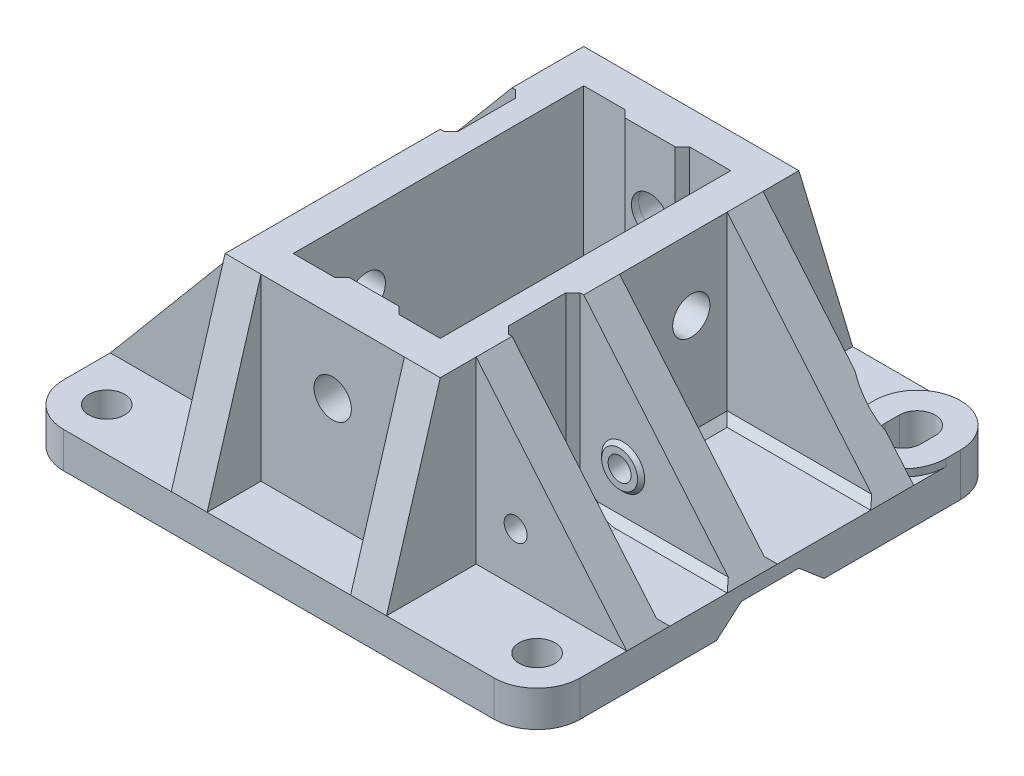
SolidWorks part; units mm, degrees
ref_plane "Front Plane" through (0, 0, 0) normal (0, 0, 1) x (1, 0, 0)
ref_plane "Top Plane" through (0, 0, 0) normal (0, 1, 0) x (1, 0, 0)
ref_plane "Right Plane" through (0, 0, 0) normal (1, 0, 0) x (0, 0, -1)
sketch "Sketch1" plane through (0, 0, 0) normal (0, 1, 0) x (1, 0, 0)
  line L0 (0, 0) -> (0, 65)
  line L1 (0, 0) -> (72, 0)
  line L2 (0, 65) -> (72, 65)
  line L3 (72, 0) -> (72, 65)
  dimension "D1" = 72
  dimension "D2" = 65
extrude "Boss-Extrude1" add sketch "Sketch1" along normal blind 5
sketch "Sketch2" plane through (0, 5, 0) normal (0, 1, 0) x (1, 0, 0)
  line L0 (21, 57.5) -> (21, 7.5)
  line L1 (21, 57.5) -> (51, 57.5)
  line L2 (21, 7.5) -> (51, 7.5)
  line L3 (51, 57.5) -> (51, 7.5)
  line L4 (0, 0) -> (72, 0) construction
  line L7 (72, 0) -> (72, 65) construction
  dimension "D1" = 50
  dimension "D2" = 7.5
  dimension "D3" = 30
  dimension "D4" = 21
extrude "Boss-Extrude2" add sketch "Sketch2" along normal blind 25
sketch "Sketch4" plane through (0, 30, 0) normal (0, 1, 0) x (1, 0, 0)
  line L0 (25.75, 52.75) -> (25.75, 12.25)
  line L1 (25.75, 52.75) -> (46.25, 52.75)
  line L2 (25.75, 12.25) -> (46.25, 12.25)
  line L3 (46.25, 52.75) -> (46.25, 12.25)
  line L4 (51, 57.5) -> (21, 57.5) construction
  line L6 (21, 57.5) -> (21, 7.5) construction
  dimension "D1" = 40.5
  dimension "D2" = 4.75
  dimension "D3" = 20.5
  dimension "D4" = 4.75
extrude "Cut-Extrude1" cut sketch "Sketch4" against normal blind 25
sketch "Sketch5" plane through (51, 0, 0) normal (1, 0, 0) x (0, 0, -1)
  line L0 (57.5, 30) -> (65, 5)
  line L1 (57.5, 5) -> (65, 5)
  line L2 (57.5, 5) -> (57.5, 30)
extrude "Boss-Extrude3" add sketch "Sketch5" against normal blind 5
ref_plane "Plane1" through (36, 0, 0) normal (1, 0, 0) x (0, 0, -1)
mirror "Mirror1" about plane through (36, 0, 0) normal (1, 0, 0) of "Boss-Extrude3"
ref_plane "Plane2" through (0, 0, -32.5) normal (0, 0, 1) x (1, 0, 0)
mirror "Mirror2" about plane through (0, 0, -32.5) normal (0, 0, 1) of "Mirror1", "Boss-Extrude3"
sketch "Sketch6" plane through (0, 0, -7.5) normal (0, 0, 1) x (1, 0, 0)
  line L0 (51, 30) -> (72, 5)
  line L1 (72, 5) -> (51, 5)
  line L2 (51, 5) -> (51, 30)
extrude "Boss-Extrude4" add sketch "Sketch6" against normal blind 5 from offset 5 offset against normal yes
mirror "Mirror3" about plane through (0, 0, -32.5) normal (0, 0, 1) of "Boss-Extrude4"
sketch "Sketch7" plane through (0, 0, -32.5) normal (0, 0, 1) x (1, 0, 0)
  line L0 (51, 30) -> (72, 5)
  line L1 (72, 5) -> (51, 5)
  line L2 (51, 5) -> (51, 30)
extrude "Boss-Extrude5" add sketch "Sketch7" along normal blind 5
mirror "Mirror4" about plane through (36, 0, 0) normal (1, 0, 0) of "Boss-Extrude4", "Mirror3"
sketch "Sketch8" plane through (0, 0, -32.5) normal (0, 0, 1) x (1, 0, 0)
  line L0 (21, 30) -> (0, 5)
  line L1 (0, 5) -> (21, 5)
  line L2 (21, 5) -> (21, 30)
extrude "Boss-Extrude6" add sketch "Sketch8" against normal blind 5
fillet "Fillet1" radius 6 4 edges at (0, 2.5, -65) (0, 2.5, 0) (72, 2.5, 0) (72, 2.5, -65)
sketch "Sketch9" plane through (0, 5, 0) normal (0, 1, 0) x (1, 0, 0)
  line L0 (63.5, 59) -> (63.5, 57)
  line L1 (68.5, 57) -> (68.5, 59)
  line L2 (60, 59) -> (60, 57)
  line L3 (72, 59) -> (72, 57)
  arc A1 (72, 59) -> (60, 59) centre (66, 59) ccw
  arc A2 (63.5, 57) -> (68.5, 57) centre (66, 57) ccw
  arc A3 (68.5, 59) -> (63.5, 59) centre (66, 59) ccw
  arc A4 (72, 59) -> (66, 65) centre (66, 59) ccw construction
  arc A6 (60, 57) -> (72, 57) centre (66, 57) ccw
  point P1 (68.5, 58)
  point P3 (72, 58)
  point P4 (66, 61.5)
  dimension "D1" = 12
  dimension "D2" = 12
  dimension "D3" = 5
  dimension "D4" = 5
  dimension "D5" = 2
  dimension "D6" = 2
  dimension "D7" = 2
  dimension "D8" = 3.5
  dimension "D9" = 3.5
sketch "Sketch10" plane through (72, 0, 0) normal (1, 0, 0) x (0, 0, -1)
  line L0 (36.5, 3) -> (32.5, 3)
  line L1 (0, 0) -> (65, 0) construction
  line L2 (32.5, 5) -> (47.5, 5) construction
  line L3 (36.5, 3) -> (40, 0)
  line L5 (32.5, 5) -> (32.5, 30) construction
  line L6 (28.5, 3) -> (25, 0)
  line L7 (28.5, 3) -> (32.5, 3)
  line L8 (25, 0) -> (40, 0)
  line M7 (6, 0) -> (59, 0)
  dimension "D1" = 4
  dimension "D2" = 25
  dimension "D3" = 3.5
  dimension "D4" = 2
extrude "Cut-Extrude3" cut sketch "Sketch10" against normal blind 75 contours L7 L6 L3 L0 M7
sketch "Sketch11" plane through (0, 5, 0) normal (0, 1, 0) x (1, 0, 0)
  line L0 (51, 0) -> (66, 0) construction
  line L1 (72, 0) -> (72, 65) construction
  circle A0 centre (66, 6) radius 2.5
  dimension "D1" = 5
  dimension "D2" = 6
  dimension "D3" = 6
extrude "Cut-Extrude4" cut sketch "Sketch11" against normal blind 5
mirror "Mirror6" about plane through (36, 0, 0) normal (1, 0, 0) of "Cut-Extrude4"
sketch "Sketch12" plane through (0, 0, -12.5) normal (0, 0, 1) x (1, 0, 0)
  line L0 (51, 30) -> (51, 5) construction
  line L1 (51, 5) -> (72, 5) construction
  circle A0 centre (56.5, 12) radius 1.6
  dimension "D1" = 3.2
  dimension "D2" = 5.5
  dimension "D3" = 7
extrude "Cut-Extrude5" cut sketch "Sketch12" against normal blind 5
sketch "Sketch13" plane through (0, 0, -7.5) normal (0, 0, 1) x (1, 0, 0)
  line L0 (26, 30) -> (46, 30) construction
  line L1 (46, 5) -> (46, 30) construction
  circle A0 centre (36, 20) radius 2.6021
  dimension "D1" = 5.2043
  dimension "D2" = 10
  dimension "D3" = 10
extrude "Cut-Extrude6" cut sketch "Sketch13" against normal blind 7
sketch "Sketch14" plane through (0, 0, -12.25) normal (0, 0, -1) x (-1, 0, 0)
  line L0 (-32.5, 30) -> (-32.5, 5)
  line L1 (-32.5, 30) -> (-39.5, 30)
  line L2 (-32.5, 5) -> (-39.5, 5)
  line L3 (-39.5, 30) -> (-39.5, 5)
  line L4 (-25.75, 30) -> (-46.25, 30) construction
  line L5 (-25.75, 5) -> (-46.25, 5) construction
  dimension "D1" = 7
  dimension "D2" = 6.75
extrude "Boss-Extrude7" add sketch "Sketch14" along normal blind 1
sketch "Sketch15" plane through (0, 30, 0) normal (0, 1, 0) x (1, 0, 0)
  line L0 (39.5, 13.25) -> (40.5, 12.25)
  line L1 (39.5, 12.25) -> (46.25, 12.25) construction
  line L2 (40.5, 12.25) -> (39.5, 12.25)
  line L3 (39.5, 12.25) -> (39.5, 13.25)
  dimension "D1" = 1
extrude "Boss-Extrude8" add sketch "Sketch15" against normal blind 25
mirror "Mirror7" about plane through (36, 0, 0) normal (1, 0, 0) of "Boss-Extrude8"
mirror "Mirror8" about plane through (0, 0, -32.5) normal (0, 0, 1) of "Cut-Extrude6", "Boss-Extrude7", "Mirror7", "Boss-Extrude8"
sketch "Sketch16" plane through (0, 0, -12.25) normal (0, 0, 1) x (1, 0, 0)
  circle A0 centre (36, 20) radius 2.6
  dimension "D1" = 5.2
extrude "Cut-Extrude7" cut sketch "Sketch16" against normal blind 65
ref_plane "Plane3" through (72, 5, -52.5) normal (0, 0, -1) x (-1, 0, 0)
sketch "Sketch21" plane through (0, 30, 0) normal (0, 1, 0) x (1, 0, 0)
  line L0 (21.5, 47.5) -> (22.5, 46.5)
  line L1 (22.5, 46.5) -> (22.5, 38.5)
  line L2 (21, 47.5) -> (21.5, 47.5)
  line L3 (21, 47.5) -> (21, 37.5) construction
  line L4 (21, 47.5) -> (21, 37.5)
  line L5 (21.5, 37.5) -> (22.5, 38.5)
  line L6 (21, 37.5) -> (21.5, 37.5)
  point P9 (21, 42.5)
  dimension "D2" = 0.5
  dimension "D3" = 135
extrude "Cut-Extrude8" cut sketch "Sketch21" against normal blind 25 and the other way through all
fillet "Fillet5" radius 7 3 edges at (22, 5, -38) (22.5, 5, -42.5) (22, 5, -47)
sketch "Sketch22" plane through (0, 30, 0) normal (0, 1, 0) x (1, 0, 0)
  line L0 (51, 17.5) -> (50.4994, 17.5)
  line L1 (50.4994, 17.5) -> (49.4994, 18.5)
  line L2 (49.4994, 18.5) -> (49.4994, 26.5)
  line L5 (51, 27.5) -> (50.4994, 27.5)
  line L6 (50.4994, 27.5) -> (49.4994, 26.5)
  line L7 (51, 17.5) -> (51, 27.5)
  dimension "D1" = 0.5006
  dimension "D2" = 1
  dimension "D3" = 135
extrude "Cut-Extrude9" cut sketch "Sketch22" against normal blind 25
fillet "Fillet6" radius 7 3 edges at (49.9994, 5, -18) (49.4994, 5, -22.5) (49.9994, 5, -27)
sketch "Sketch23" plane through (72, 0, 0) normal (1, 0, 0) x (0, 0, -1)
  line L0 (17.5, 5) -> (17.5, 5.9984)
  line L1 (17.5, 5) -> (18.5023, 5)
  line L2 (17.5, 5) -> (27.5, 5) construction
  line L3 (18.5023, 5) -> (17.5, 5.9984)
extrude "Boss-Extrude10" add sketch "Sketch23" against normal blind 25
sketch "Sketch24" plane through (72, 0, 0) normal (1, 0, 0) x (0, 0, -1)
  line L0 (27.5, 5) -> (27.5, 6)
  line L1 (27.5, 6) -> (26.5, 5)
  line L2 (18.5023, 5) -> (27.5, 5) construction
  line L3 (26.5, 5) -> (27.5, 5)
  dimension "D1" = 1
  dimension "D2" = 1
extrude "Boss-Extrude11" add sketch "Sketch24" against normal blind 25
sketch "Sketch25" plane through (0, 0, -32.5) normal (0, 0, -1) x (-1, 0, 0)
  line L0 (-51, 5) -> (-51, 5.9978)
  line L1 (-51, 30) -> (-51, 5) construction
  line L2 (-51, 5.9978) -> (-52, 5)
  line L3 (-51, 5) -> (-72, 5) construction
  line L4 (-52, 5) -> (-51, 5)
  dimension "D1" = 1
extrude "Boss-Extrude12" add sketch "Sketch25" along normal blind 15
sketch "Sketch26" plane through (72, 0, 0) normal (1, 0, 0) x (0, 0, -1)
  line L0 (32.5, 5) -> (32.5, 5.9972)
  line L1 (32.5, 5.9972) -> (33.5, 5)
  line L2 (32.5, 5) -> (47.5, 5) construction
  line L3 (33.5, 5) -> (32.5, 5)
  dimension "D1" = 1
extrude "Boss-Extrude13" add sketch "Sketch26" against normal blind 25
sketch "Sketch27" plane through (72, 0, 0) normal (1, 0, 0) x (0, 0, -1)
  line L0 (47.5, 5) -> (47.5, 6)
  line L1 (47.5, 6) -> (46.5, 5)
  line L2 (33.5, 5) -> (47.5, 5) construction
  line L3 (46.5, 5) -> (47.5, 5)
  dimension "D1" = 1
  dimension "D2" = 1
extrude "Boss-Extrude14" add sketch "Sketch27" against normal blind 25
ref_plane "Plane4" through (44.6764, 37.5281, 0) normal (0.7657, 0.6432, 0) x (0, 0, -1)
sketch "Sketch28" plane through (44.6764, 37.5281, 0) normal (0.7657, 0.6432, 0) x (0, 0, -1)
  line L0 (11.4122, -43.5785) -> (50.5755, -43.5785)
  line L1 (11.4122, -43.5785) -> (11.4122, -35.2711)
  line L2 (50.5755, -43.5785) -> (50.5755, -35.2711)
  line L3 (11.4122, -35.2711) -> (50.5755, -35.2711)
extrude "Cut-Extrude10" cut sketch "Sketch28" along normal blind 5
sketch "Sketch29" plane through (0, 0, 0) normal (-1, 0, 0) x (0, 0, 1)
  line L0 (-47.5, 5) -> (-47.5, 6)
  line L1 (-47.5, 6) -> (-46.5, 5)
  line L2 (-47.5, 5) -> (-37.5, 5) construction
  line L3 (-46.5, 5) -> (-47.5, 5)
  line L4 (-37.5, 5) -> (-37.5, 6)
  line L5 (-37.5, 6) -> (-38.5, 5)
  line L6 (-38.5, 5) -> (-37.5, 5)
  dimension "D1" = 1
  dimension "D2" = 1
  dimension "D3" = 1
  dimension "D4" = 1
extrude "Boss-Extrude15" add sketch "Sketch29" against normal blind 25
sketch "Sketch30" plane through (0, 0, -32.5) normal (0, 0, 1) x (1, 0, 0)
  line L0 (21, 5) -> (20, 5)
  line L1 (0, 5) -> (21, 5) construction
  line L2 (20, 5) -> (21, 6)
  line L3 (21, 5) -> (21, 30) construction
  line L4 (21, 6) -> (21, 5)
  dimension "D1" = 1
  dimension "D2" = 1
extrude "Boss-Extrude16" add sketch "Sketch30" along normal blind 15
sketch "Sketch31" plane through (0, 0, 0) normal (-1, 0, 0) x (0, 0, 1)
  line L0 (-32.5, 5) -> (-32.5, 6)
  line L1 (-32.5, 6) -> (-31.5, 5)
  line L2 (-32.5, 5) -> (-17.5, 5) construction
  line L3 (-31.5, 5) -> (-32.5, 5)
  line L4 (-17.5, 5) -> (-17.5, 6.0006)
  line L5 (-17.5, 6.0006) -> (-18.5006, 5)
  line L6 (-18.5006, 5) -> (-17.5, 5)
  dimension "D1" = 1.0006
  dimension "D2" = 1.0006
  dimension "D3" = 1
  dimension "D4" = 1
extrude "Boss-Extrude17" add sketch "Sketch31" against normal blind 25
mirror "Mirror10" about plane through (36, 0, 0) normal (1, 0, 0) of "Cut-Extrude10"
sketch "Sketch32" plane through (0, 0, -17.5) normal (0, 0, -1) x (-1, 0, 0)
  circle A0 centre (-56.5, 12) radius 3
  dimension "D1" = 6
extrude "Boss-Extrude18" add sketch "Sketch32" along normal blind 0.5 draft 45
sketch "Sketch33" plane through (0, 0, -12.5) normal (0, 0, 1) x (1, 0, 0)
  circle A0 centre (56.5, 12) radius 1.6
extrude "Cut-Extrude11" cut sketch "Sketch33" against normal blind 20.5
sketch "Sketch34" plane through (0, 0, -27.5) normal (0, 0, 1) x (1, 0, 0)
  circle A0 centre (56.5, 12) radius 3
  dimension "D1" = 6
extrude "Boss-Extrude19" add sketch "Sketch34" along normal blind 0.5 draft 45
sketch "Sketch35" plane through (0, 0, -32.5) normal (0, 0, -1) x (-1, 0, 0)
  circle A0 centre (-56.5, 12) radius 1.6
extrude "Cut-Extrude12" cut sketch "Sketch35" against normal blind 10.5
sketch "Sketch36" plane through (0, 0, -52.5) normal (0, 0, -1) x (-1, 0, 0)
  line L0 (-21, 30) -> (-21, 5) construction
  line L1 (-21, 5) -> (0, 5) construction
  circle A0 centre (-15.5, 12) radius 1.6
  dimension "D1" = 3.2
  dimension "D2" = 5.5
  dimension "D3" = 7
sketch "Sketch37" plane through (0, 0, -47.5) normal (0, 0, 1) x (1, 0, 0)
  circle A0 centre (15.5, 12) radius 3
  dimension "D1" = 6
extrude "Boss-Extrude20" add sketch "Sketch37" along normal blind 0.5 draft 45
sketch "Sketch38" plane through (0, 0, -37.5) normal (0, 0, -1) x (-1, 0, 0)
  circle A0 centre (-15.5, 12) radius 3
  dimension "D1" = 6
extrude "Boss-Extrude21" add sketch "Sketch38" along normal blind 0.5 draft 45
extrude "Cut-Extrude13" cut sketch "Sketch36" against normal blind 20.5
sketch "Sketch40" plane through (21, 0, 0) normal (-1, 0, 0) x (0, 0, 1)
  line L1 (-32.5, 30) -> (-17.5, 30) construction
  line L2 (-17.5, 30) -> (-17.5, 6.0006) construction
  circle A0 centre (-22.5, 20) radius 2.6
  dimension "D1" = 5.2
  dimension "D3" = 5
  dimension "D2" = 10
extrude "Cut-Extrude14" cut sketch "Sketch40" against normal blind 10
sketch "Sketch41" plane through (51, 0, 0) normal (1, 0, 0) x (0, 0, -1)
  line L0 (32.5, 30) -> (47.5, 30) construction
  line L1 (47.5, 30) -> (47.5, 6) construction
  circle A0 centre (42.5, 20) radius 2.6
  point P4 (40, 30)
  dimension "D1" = 5.2
  dimension "D2" = 10
  dimension "D3" = 5
extrude "Cut-Extrude15" cut sketch "Sketch41" against normal blind 10
extrude "Boss-Extrude22" add sketch "Sketch9" along normal blind 1
sketch "Sketch42" plane through (0, 6, 0) normal (0, 1, 0) x (1, 0, 0)
  line L0 (66, 65) -> (72, 65)
  line L1 (72, 65) -> (59.4165, 65)
  arc A0 (72, 59) -> (60, 59) centre (66, 59) ccw construction
ref_plane "Plane5" through (0, 0.8221, 0.0654) normal (0, 0.9968, 0.0793) x (-1, 0, 0)
sketch "Sketch45" plane through (0, 6, 0) normal (0, 1, 0) x (1, 0, 0)
  line L0 (68.1794, 52.5) -> (63.8076, 52.5063)
  line L1 (62.0314, 52.5) -> (69.9686, 52.5) construction
  arc A0 (63.8076, 52.5063) -> (68.1794, 52.5) centre (66, 57) ccw
  dimension "D1" = 10
extrude "Cut-Extrude17" cut sketch "Sketch45" along normal blind 11
sketch "Sketch47" plane through (0, 5, 0) normal (0, 1, 0) x (1, 0, 0)
  line L0 (68.5, 59) -> (68.5, 57)
  line L1 (63.5, 57) -> (63.5, 59)
  arc A0 (63.5, 57) -> (68.5, 57) centre (66, 57) ccw
  arc A1 (68.5, 59) -> (63.5, 59) centre (66, 59) ccw
extrude "Cut-Extrude18" cut sketch "Sketch47" against normal blind 10
mirror "Mirror12" about plane through (36, 0, 0) normal (1, 0, 0) of "Cut-Extrude17", "Boss-Extrude22"
